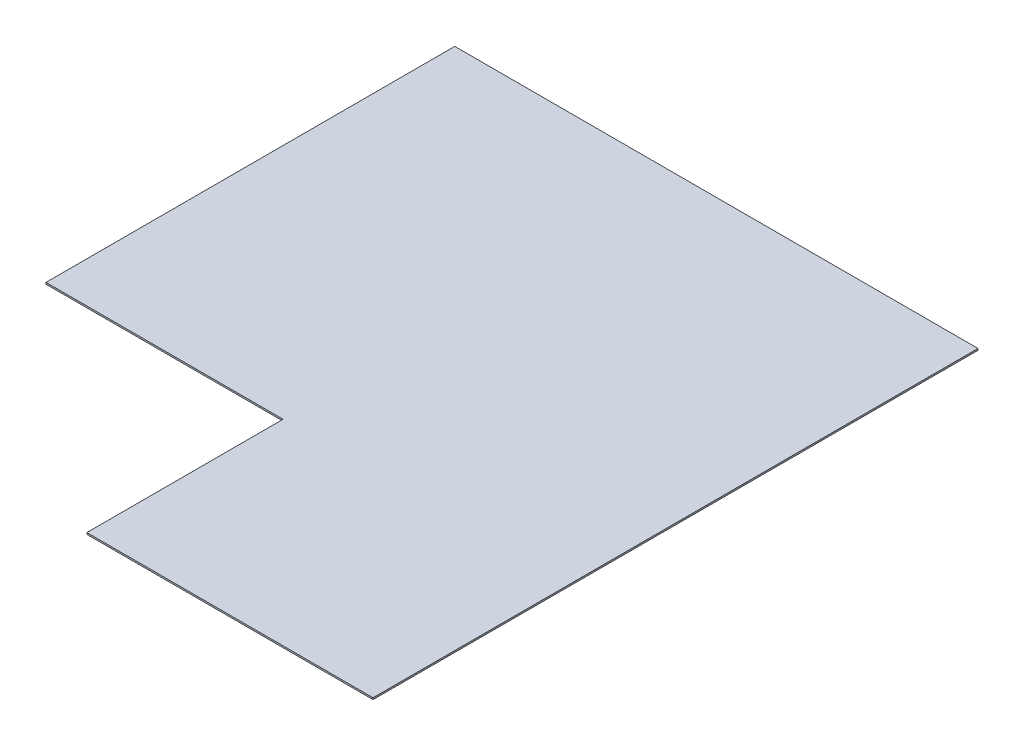
SolidWorks part; units mm, degrees
material "Pine"
ref_plane "Front Plane" through (0, 0, 0) normal (0, 0, 1) x (1, 0, 0)
ref_plane "Top Plane" through (0, 0, 0) normal (0, 1, 0) x (1, 0, 0)
ref_plane "Right Plane" through (0, 0, 0) normal (1, 0, 0) x (0, 0, -1)
sketch "Sketch1" plane through (0, 0, 0) normal (0, 1, 0) x (1, 0, 0)
  line L0 (0, 0) -> (-1016, 0)
  line L1 (-1016, 0) -> (-1016, -793.75)
  line L2 (-1016, -793.75) -> (-555.625, -793.75)
  line L3 (-555.625, -793.75) -> (-555.625, -1174.75)
  line L4 (-555.625, -1174.75) -> (0, -1174.75)
  line L5 (0, -1174.75) -> (0, 0)
  dimension "D1" = 381
  dimension "D2" = 460.375
  dimension "D3" = 1016
  dimension "D4" = 1174.75
extrude "Boss-Extrude1" add sketch "Sketch1" along normal blind 3.175
